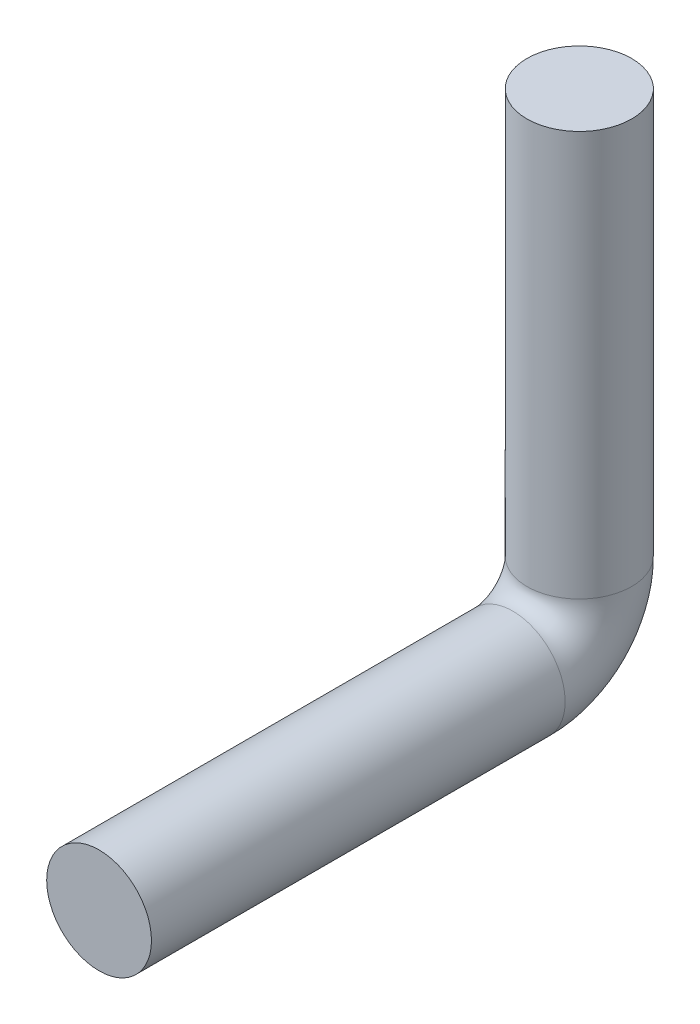
SolidWorks part; units mm, degrees
ref_plane "Front Plane" through (0, 0, 0) normal (0, 0, 1) x (1, 0, 0)
ref_plane "Top Plane" through (0, 0, 0) normal (0, 1, 0) x (1, 0, 0)
ref_plane "Right Plane" through (0, 0, 0) normal (1, 0, 0) x (0, 0, -1)
sketch "Sketch1" plane through (0, 0, 0) normal (0, 1, 0) x (1, 0, 0)
  circle A0 centre (0, 0) radius 30
  dimension "D1" = 60
sketch "Sketch2" plane through (0, 0, 0) normal (1, 0, 0) x (0, 0, -1)
  line L1 (0, 0) -> (0, -231.9)
  line L2 (-38.1, -270) -> (-275, -270)
  arc A0 (0, -231.9) -> (-38.1, -270) centre (-38.1, -231.9) cw
  point P5 (0, -270)
  dimension "D3" = 38.1
  dimension "D1" = 270
  dimension "D2" = 275
sweep "Sweep1" add profiles "Sketch1" path "Sketch2"
